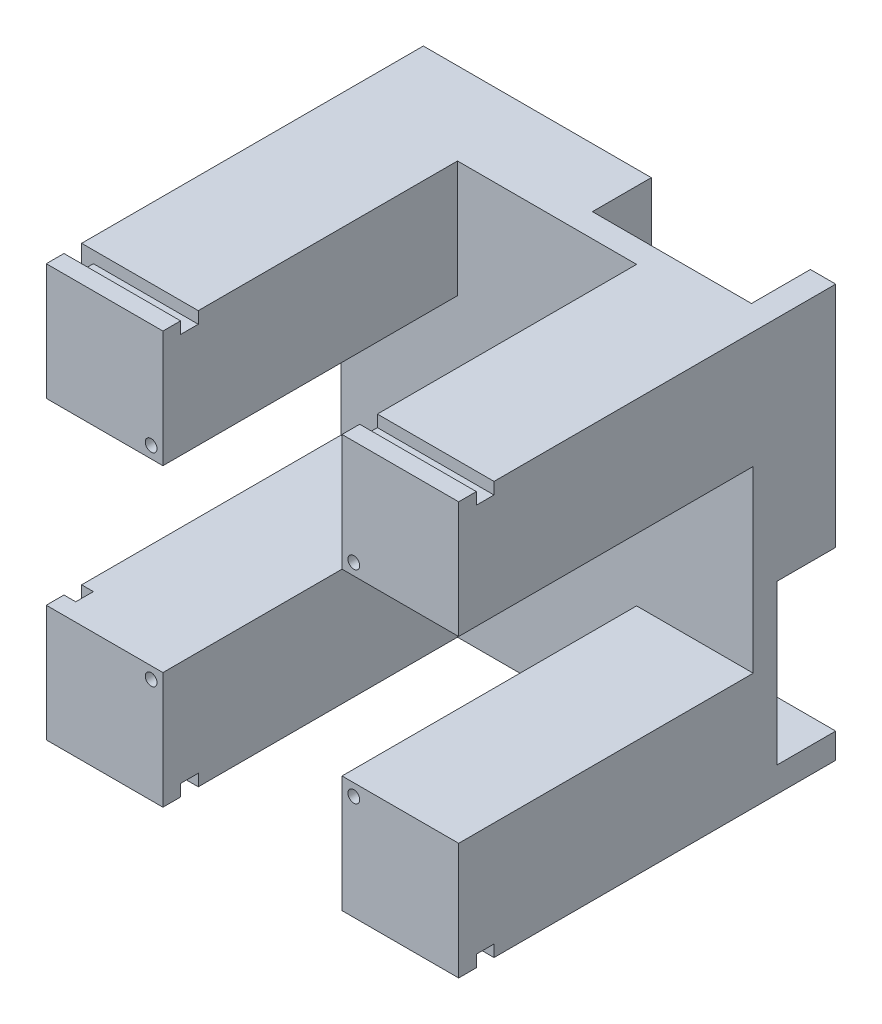
SolidWorks part; units mm, degrees
ref_plane "Plan de face" through (0, 0, 0) normal (0, 0, 1) x (1, 0, 0)
ref_plane "Plan de dessus" through (0, 0, 0) normal (0, 1, 0) x (1, 0, 0)
ref_plane "Plan de droite" through (0, 0, 0) normal (1, 0, 0) x (0, 0, -1)
sketch "Esquisse1" plane through (0, 0, 0) normal (0, 0, 1) x (1, 0, 0)
  line L1 (0, 0) -> (-70, 0)
  line L2 (0, 0) -> (0, 70)
  line L3 (0, 70) -> (-70, 70)
  line L4 (-70, 0) -> (-70, 70)
  dimension "D1" = 70
  dimension "D2" = 70
extrude "Boss.-Extru.1" add sketch "Esquisse1" along normal blind 64
sketch "Esquisse2" plane through (0, 0, 64) normal (0, 0, 1) x (1, 0, 0)
  line L0 (-70, 70) -> (-70, 0) construction
  line L1 (-70, 50.2) -> (0, 50.2)
  line L2 (-70, 50.2) -> (-70, 19.8)
  line L3 (-70, 19.8) -> (0, 19.8)
  line L4 (0, 50.2) -> (0, 19.8)
  line L5 (0, 0) -> (0, 70) construction
  line L6 (-70, 0) -> (0, 0) construction
  line L7 (-19.8, 0) -> (-50.2, 0)
  line L8 (-19.8, 0) -> (-19.8, 70)
  line L9 (-19.8, 70) -> (-50.2, 70)
  line L10 (-50.2, 0) -> (-50.2, 70)
  line L11 (0, 70) -> (-70, 70) construction
  line M5 (0, 0) -> (0, 70)
  line M6 (0, 70) -> (-70, 70)
  line M7 (-70, 70) -> (-70, 0)
  line M8 (-70, 0) -> (0, 0)
  dimension "D1" = 30.4
  dimension "D2" = 19.8
  dimension "D3" = 30.4
  dimension "D4" = 19.8
extrude "Enlèv. mat.-Extru.1" cut sketch "Esquisse2" against normal blind 50 contours L10 L1 L8 M6 | L10 L3 L8 L1 | L8 L3 L1 M5 | L3 L10 L1 M7 | L10 L8 L3 M8
sketch "Esquisse5" plane through (-70, 0, 0) normal (-1, 0, 0) x (0, 0, 1)
  line L0 (64, 70) -> (0, 70) construction
  line L1 (61, 70) -> (58, 70)
  line L2 (61, 70) -> (61, 68)
  line L3 (61, 68) -> (58, 68)
  line L4 (58, 70) -> (58, 68)
  line L5 (64, 0) -> (0, 0) construction
  line L6 (61, 0) -> (58, 0)
  line L7 (61, 0) -> (61, 2)
  line L8 (61, 2) -> (58, 2)
  line L9 (58, 0) -> (58, 2)
  line L10 (64, 19.8) -> (64, 0) construction
  line L11 (64, 70) -> (64, 50.2) construction
  dimension "D1" = 3
  dimension "D2" = 3
  dimension "D3" = 2
  dimension "D4" = 2
  dimension "D5" = 3
  dimension "D6" = 3
extrude "Enlèv. mat.-Extru.3" cut sketch "Esquisse5" against normal through all
sketch "Esquisse6" plane through (0, 70, 0) normal (0, 1, 0) x (1, 0, 0)
  line L0 (-50.2, -61) -> (-70, -61) construction
  line L1 (-70, -58) -> (-68, -58)
  line L2 (-70, -58) -> (-70, -61)
  line L3 (-70, -61) -> (-68, -61)
  line L4 (-68, -58) -> (-68, -61)
  dimension "D1" = 2
extrude "Enlèv. mat.-Extru.4" cut sketch "Esquisse6" against normal through all
sketch "Esquisse7" plane through (0, 0, 64) normal (0, 0, 1) x (1, 0, 0)
  line L0 (-50.2, 0) -> (-50.2, 19.8) construction
  line L1 (-70, 19.8) -> (-50.2, 19.8) construction
  circle A0 centre (-52.2, 17.8) radius 1
  dimension "D1" = 2
  dimension "D2" = 2
  dimension "D3" = 2
extrude "Enlèv. mat.-Extru.5" cut sketch "Esquisse7" against normal through all
sketch "Esquisse8" plane through (0, 0, 0) normal (0, 0, -1) x (-1, 0, 0)
  line L0 (60.2, 17.8) -> (60.2, 0)
  line L1 (70, 0) -> (0, 0) construction
  line L2 (60.2, 0) -> (44.2, 0)
  line L3 (44.2, 0) -> (44.2, 17.8)
  line L4 (44.2, 17.8) -> (60.2, 17.8)
  circle A0 centre (52.2, 17.8) radius 8
  circle M2 centre (52.2, 17.8) radius 1
  line M4 (0, 0) -> (70, 0)
  dimension "D1" = 16
extrude "Enlèv. mat.-Extru.7" cut sketch "Esquisse8" against normal blind 10 contours A0 L3 L0 M4 | L4 A0 M2 | L4 A0 M2
sketch "Esquisse9" plane through (0, 0, 0) normal (0, 0, -1) x (-1, 0, 0)
  line L0 (46.2, 17.8) -> (46.2, 0)
  line L1 (46.2, 0) -> (44.2, 0)
  line L2 (44.2, 0) -> (44.2, 28.7424)
  line L3 (44.2, 28.7424) -> (60.1757, 28.7424)
  line L4 (60.1757, 28.7424) -> (60.2, 17.8)
  line L5 (60.2, 17.8) -> (60.2, 0)
  line L6 (60.2, 17.8) -> (60.2, 0) construction
  line L7 (58.2, 17.8) -> (58.2, 0)
  line L8 (58.2, 0) -> (60.2, 0)
  circle A0 centre (52.2, 17.8) radius 6
  line M1 (60.2, 17.8) -> (60.2, 0)
  line M7 (44.2, 0) -> (44.2, 17.8)
  arc M8 (44.2, 17.8) -> (60.2, 17.8) centre (52.2, 17.8) cw
  dimension "D1" = 12
extrude "Boss.-Extru.2" add sketch "Esquisse9" against normal blind 3.8 contours A0 L7 L8 L1 L0 M1 M8 M7
sketch "Esquisse10" plane through (0, 0, 0) normal (0, 0, -1) x (-1, 0, 0)
  line L0 (70, 0) -> (58.2, 0) construction
  line L1 (38.7, 18.1) -> (65.7, 18.1)
  line L2 (38.7, 18.1) -> (38.7, 0)
  line L3 (38.7, 0) -> (65.7, 0)
  line L4 (65.7, 18.1) -> (65.7, 0)
  arc A0 (58.1926, 18.098) -> (46.2076, 18.1013) centre (52.2, 17.8) ccw
  arc A2 (58.2, 17.8) -> (46.2, 17.8) centre (52.2, 17.8) ccw construction
  line M3 (58.2, 17.8) -> (58.2, 0)
  line M4 (58.2, 0) -> (70, 0)
  line M8 (0, 0) -> (46.2, 0)
  line M9 (46.2, 0) -> (46.2, 17.8)
  dimension "D1" = 27
  dimension "D2" = 5.5
extrude "Enlèv. mat.-Extru.8" cut sketch "Esquisse10" against normal blind 10 contours L1 L2 M8 M9 | L4 L1 M3 M4
sketch "Esquisse11" plane through (0, 18.1, 0) normal (0, -1, 0) x (1, 0, 0)
  line L0 (-38.7, 10) -> (-38.7, 0) construction
  line L1 (-65.7, 10) -> (-65.7, 0) construction
  line L2 (-60.1944, 10) -> (-65.7, 10) construction
  line L3 (-38.7, 10) -> (-44.2056, 10) construction
  circle A0 centre (-41.7, 7) radius 1.25
  circle A1 centre (-62.7, 7) radius 1.25
  dimension "D1" = 2.5
  dimension "D2" = 2.5
  dimension "D3" = 3
  dimension "D4" = 3
  dimension "D5" = 3
  dimension "D6" = 3
extrude "Enlèv. mat.-Extru.9" cut sketch "Esquisse11" against normal blind 15
sketch3d "Esquisse3D2"
  line L0 (-35, 35, 57.383) -> (-35, 35, -1.6203) construction
  point P2 (0, 35, 0)
  point P5 (0, 35, 64)
  dimension "D1" = 35
  dimension "D2" = 35
  dimension "D3" = 35
pattern_circular "Répétition circulaire1" count 4 every 90 about axis through (-35, 35, 0) along (0, 0, 1) of "Enlèv. mat.-Extru.5", "Enlèv. mat.-Extru.7", "Enlèv. mat.-Extru.8"
